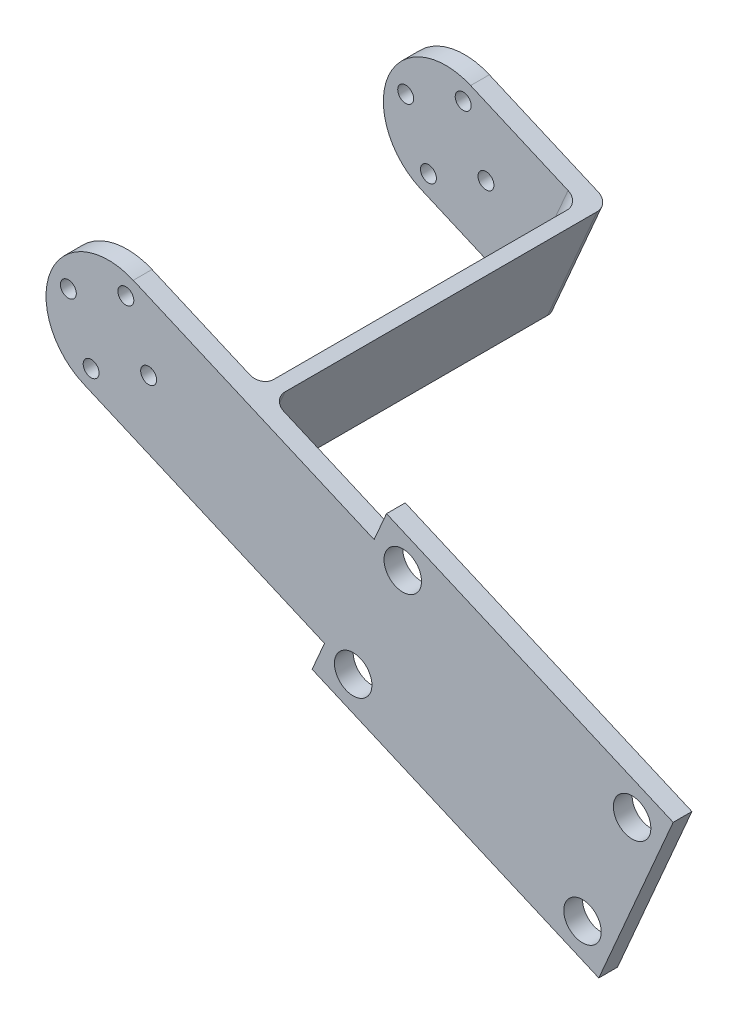
SolidWorks part; units mm, degrees
ref_plane "Plan de face" through (0, 0, 0) normal (0, 0, 1) x (1, 0, 0)
ref_plane "Plan de dessus" through (0, 0, 0) normal (0, 1, 0) x (1, 0, 0)
ref_plane "Plan de droite" through (0, 0, 0) normal (1, 0, 0) x (0, 0, -1)
sketch "Esquisse2" plane through (0, 0, -10.7555) normal (0, 0, 1) x (1, 0, 0)
  line L1 (42.5187, -7.494) -> (3.9696, 9.1784)
  line L2 (34.5795, -25.8507) -> (-3.9696, -9.1784)
  line L4 (19.4563, 2.4804) -> (11.5171, -15.8763) construction
  line L5 (15.4867, -6.6979) -> (-9.1784, 3.9696) construction
  line L7 (32.5947, -30.4399) -> (34.5795, -25.8507)
  line L8 (32.5947, -30.4399) -> (78.4865, -50.2879)
  line L9 (44.5035, -2.9048) -> (90.3953, -22.7528)
  line L10 (78.4865, -50.2879) -> (90.3953, -22.7528)
  line L14 (42.5187, -7.494) -> (44.5035, -2.9048)
  arc A0 (3.9696, 9.1784) -> (-3.9696, -9.1784) centre (0, 0) ccw
  circle A3 centre (6.4249, -2.7787) radius 1.275
  circle A6 centre (-2.7787, -6.4249) radius 1.275
  circle A8 centre (-6.4249, 2.7787) radius 1.275
  circle A10 centre (2.7787, 6.4249) radius 1.275
  circle A11 centre (75.8821, -43.7139) radius 3
  circle A13 centre (83.8213, -25.3572) radius 3
  circle A15 centre (47.1079, -9.4788) radius 3
  circle A17 centre (39.1687, -27.8355) radius 3
  point P20 (0, 0)
  dimension "D2" = 6
  dimension "D3" = 10
  dimension "D4" = 3.9696
  dimension "D5" = 4
  dimension "D6" = 5
  dimension "D8" = 5
  dimension "D16" = 2.55
  dimension "D7" = 5
  dimension "D9" = 5
  dimension "D10" = 5
  dimension "D11" = 40
  dimension "D12" = 92
extrude "Boss.-Extru.1" add sketch "Esquisse2" along normal blind 3
sketch "Esquisse5" plane through (0, 0, -10.7555) normal (0, 0, -1) x (-1, 0, 0)
  line L8 (-13.4693, -16.7206) -> (-21.4085, 1.6361)
  line L9 (-15.305, -17.5145) -> (-13.4693, -16.7206)
  line L10 (-23.2442, 0.8422) -> (-15.305, -17.5145)
  line L11 (-21.4085, 1.6361) -> (-23.2442, 0.8422)
  arc A0 (3.9696, -9.1784) -> (-3.9696, 9.1784) centre (0, 0) ccw construction
  dimension "D1" = 2
  dimension "D2" = 19
extrude "Boss.-Extru.4" add sketch "Esquisse5" along normal blind 51
fillet "Congé1" radius 2 2 edges at (19.2746, -8.3362, -10.7555) (17.4389, -7.5422, -10.7555)
sketch "Esquisse6" plane through (0, 0, -61.7555) normal (0, 0, -1) x (-1, 0, 0)
  line L1 (3.9696, -9.1784) -> (-11.6336, -15.9267) construction
  line L2 (-19.5728, 2.43) -> (-3.9696, 9.1784) construction
  line L4 (3.9696, -9.1784) -> (-11.6336, -15.9267)
  line L5 (-19.5728, 2.43) -> (-3.9696, 9.1784)
  line L9 (-19.5728, 2.43) -> (-23.2442, 0.8422)
  line L10 (-23.2442, 0.8422) -> (-15.305, -17.5145)
  line L11 (-15.305, -17.5145) -> (-11.6336, -15.9267)
  circle A0 centre (6.4249, 2.7787) radius 1.275 construction
  circle A1 centre (-2.7787, 6.4249) radius 1.275 construction
  circle A2 centre (-6.4249, -2.7787) radius 1.275 construction
  circle A3 centre (2.7787, -6.4249) radius 1.275 construction
  arc A4 (3.9696, -9.1784) -> (-3.9696, 9.1784) centre (0, 0) ccw construction
  circle A5 centre (6.4249, 2.7787) radius 1.275
  circle A6 centre (-2.7787, 6.4249) radius 1.275
  circle A7 centre (-6.4249, -2.7787) radius 1.275
  circle A8 centre (2.7787, -6.4249) radius 1.275
  arc A9 (3.9696, -9.1784) -> (-3.9696, 9.1784) centre (0, 0) ccw
extrude "Boss.-Extru.5" add sketch "Esquisse6" along normal blind 3
fillet "Congé2" radius 2 2 edges at (17.4389, -7.5422, -61.7555) (19.2746, -8.3362, -64.7555)
